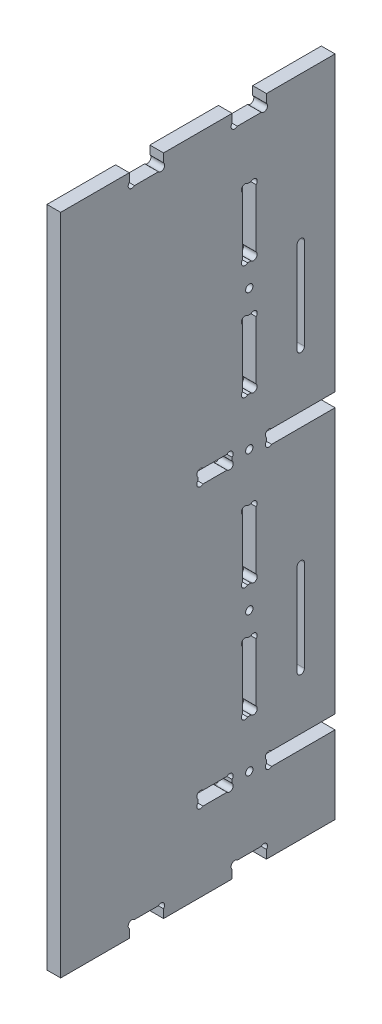
SolidWorks part; units mm, degrees
ref_plane "Plan de face" through (0, 0, 0) normal (0, 0, 1) x (1, 0, 0)
ref_plane "Plan de dessus" through (0, 0, 0) normal (0, 1, 0) x (1, 0, 0)
ref_plane "Plan de droite" through (0, 0, 0) normal (1, 0, 0) x (0, 0, -1)
sketch "Esquisse1" plane through (0, 0, 0) normal (1, 0, 0) x (0, 0, -1)
  line L0 (-10, 0) -> (130, 0) construction
  line L1 (0, -10) -> (0, 300) construction
  line L2 (120, -10) -> (120, 300) construction
  line L3 (130, 290) -> (-10, 290) construction
  line L4 (-20, 34) -> (140, 34) construction
  line L5 (-20, 40) -> (140, 40) construction
  line L6 (140, 156) -> (-20, 156) construction
  line L7 (-20, 162) -> (140, 162) construction
  line L8 (-10, 284) -> (130, 284) construction
  line L9 (130, 6) -> (-10, 6) construction
  line L10 (-20, 256) -> (140, 256) construction
  line L11 (60, 320.0265) -> (60, -23.3948) construction
  line L12 (-59.0456, 145) -> (66.7218, 145) construction
  line L13 (30, -9.1701) -> (30, 14.8573) construction
  line L14 (45, 11.6889) -> (45, -9.1701) construction
  line L15 (37.5, 2.4409) -> (37.5, -4.0751) construction
  line L16 (30, 6) -> (42.8913, -6.8913) construction
  line L17 (32.2627, 6) -> (42.7373, 6)
  line L18 (45, 3.7373) -> (45, 0)
  line L19 (30, 3.7373) -> (30, 0)
  line L20 (75, 3.7373) -> (75, 0)
  line L21 (87.7373, 6) -> (77.2627, 6)
  line L22 (90, 3.7373) -> (90, 0)
  line L23 (0, 0) -> (30, 0)
  line L24 (45, 0) -> (75, 0)
  line L25 (90, 0) -> (120, 0)
  line L26 (90, 290) -> (120, 290)
  line L27 (90, 286.2627) -> (90, 290)
  line L28 (87.7373, 284) -> (77.2627, 284)
  line L29 (75, 286.2627) -> (75, 290)
  line L30 (45, 290) -> (75, 290)
  line L31 (45, 286.2627) -> (45, 290)
  line L32 (32.2627, 284) -> (42.7373, 284)
  line L33 (30, 286.2627) -> (30, 290)
  line L34 (0, 290) -> (30, 290)
  line L35 (0, 290) -> (0, 0)
  line L36 (120, 0) -> (120, 34)
  line L37 (-20, 134) -> (66.7218, 134) construction
  line L38 (90, 310.1112) -> (90, -15.2075) construction
  line L39 (70.8381, 37) -> (93.292, 37) construction
  line L40 (79.681, 98) -> (87.7395, 98) construction
  line L41 (90, 34) -> (99.2543, 43.2543) construction
  line L42 (90, 37.7373) -> (90, 36.2627)
  line L43 (92.2627, 40) -> (120, 40)
  line L44 (92.2627, 34) -> (120, 34)
  line L45 (120, 40) -> (120, 156)
  line L46 (92.2627, 162) -> (120, 162)
  line L47 (92.2627, 156) -> (120, 156)
  line L48 (90, 158.2627) -> (90, 159.7373)
  line L49 (120, 162) -> (120, 290)
  line L50 (82.5, -10) -> (82.5, 300) construction
  line L51 (75, 43.6727) -> (75, 30.1815) construction
  line L52 (67.5, 38.4171) -> (67.5, 35.1314) construction
  line L53 (75, 37.7373) -> (75, 36.2627)
  line L54 (60, 37.7373) -> (60, 36.2627)
  line L55 (62.2627, 40) -> (72.7373, 40)
  line L56 (72.7373, 34) -> (62.2627, 34)
  line L57 (60, 158.2627) -> (60, 159.7373)
  line L58 (72.7373, 162) -> (62.2627, 162)
  line L59 (62.2627, 156) -> (72.7373, 156)
  line L60 (75, 158.2627) -> (75, 159.7373)
  line L61 (79.5, 164.7795) -> (79.5, 25.9693) construction
  line L62 (85.5, 164.7795) -> (85.5, 25.9693) construction
  line L63 (88.8686, 88) -> (51.1707, 88) construction
  line L64 (97.4677, 58) -> (51.1707, 58) construction
  line L65 (79.5, 88) -> (87.7395, 79.7605) construction
  line L66 (77.6869, 73) -> (86.5883, 73) construction
  line L67 (83.2373, 138) -> (81.7627, 138)
  line L68 (83.2373, 58) -> (81.7627, 58)
  line L69 (85.5, 60.2627) -> (85.5, 85.7373)
  line L70 (83.2373, 88) -> (81.7627, 88)
  line L71 (79.5, 60.2627) -> (79.5, 85.7373)
  line L72 (85.5, 135.7373) -> (85.5, 110.2627)
  line L73 (79.5, 135.7373) -> (79.5, 110.2627)
  line L74 (83.2373, 108) -> (81.7627, 108)
  line L75 (66.7218, 159) -> (108.1831, 159) construction
  line L76 (85.5, 257.7373) -> (85.5, 232.2627)
  line L77 (79.5, 257.7373) -> (79.5, 232.2627)
  line L78 (83.2373, 260) -> (81.7627, 260)
  line L79 (83.2373, 230) -> (81.7627, 230)
  line L80 (83.2373, 210) -> (81.7627, 210)
  line L81 (85.5, 182.2627) -> (85.5, 207.7373)
  line L82 (79.5, 182.2627) -> (79.5, 207.7373)
  line L83 (83.2373, 180) -> (81.7627, 180)
  line L84 (105, 325.8851) -> (105, -46.468) construction
  line L85 (170.2936, 84) -> (-38.142, 84) construction
  line L86 (170.2936, 206) -> (-16.5119, 206) construction
  line L87 (170.2936, 64) -> (94.9816, 64) construction
  line L88 (94.9816, 104) -> (170.2936, 104) construction
  line L89 (170.2936, 186) -> (94.9816, 186) construction
  line L90 (94.9816, 226) -> (170.2936, 226) construction
  line L91 (106.6, 104) -> (106.6, 64)
  line L92 (103.4, 64) -> (103.4, 104)
  line L93 (106.6, 226) -> (106.6, 186)
  line L94 (103.4, 186) -> (103.4, 226)
  line L98 (106.6, 234.8116) -> (106.6, 58) construction
  line L99 (103.4, 58) -> (103.4, 234.8116) construction
  arc A0 (32.2627, 6) -> (30, 3.7373) centre (31.1314, 4.8686) ccw
  arc A1 (42.7373, 6) -> (45, 3.7373) centre (43.8686, 4.8686) cw
  arc A2 (77.2627, 6) -> (75, 3.7373) centre (76.1314, 4.8686) ccw
  arc A3 (87.7373, 6) -> (90, 3.7373) centre (88.8686, 4.8686) cw
  arc A4 (87.7373, 284) -> (90, 286.2627) centre (88.8686, 285.1314) ccw
  arc A5 (77.2627, 284) -> (75, 286.2627) centre (76.1314, 285.1314) cw
  arc A6 (42.7373, 284) -> (45, 286.2627) centre (43.8686, 285.1314) ccw
  arc A7 (32.2627, 284) -> (30, 286.2627) centre (31.1314, 285.1314) cw
  arc A8 (90, 36.2627) -> (92.2627, 34) centre (91.1314, 35.1314) ccw
  arc A9 (90, 37.7373) -> (92.2627, 40) centre (91.1314, 38.8686) cw
  arc A10 (90, 158.2627) -> (92.2627, 156) centre (91.1314, 157.1314) ccw
  arc A11 (90, 159.7373) -> (92.2627, 162) centre (91.1314, 160.8686) cw
  circle A12 centre (82.5, 37) radius 1.6
  circle A13 centre (82.5, 159) radius 1.6
  arc A14 (75, 36.2627) -> (72.7373, 34) centre (73.8686, 35.1314) cw
  arc A15 (75, 37.7373) -> (72.7373, 40) centre (73.8686, 38.8686) ccw
  arc A16 (60, 36.2627) -> (62.2627, 34) centre (61.1314, 35.1314) ccw
  arc A17 (60, 37.7373) -> (62.2627, 40) centre (61.1314, 38.8686) cw
  arc A18 (60, 158.2627) -> (62.2627, 156) centre (61.1314, 157.1314) ccw
  arc A19 (60, 159.7373) -> (62.2627, 162) centre (61.1314, 160.8686) cw
  arc A20 (75, 158.2627) -> (72.7373, 156) centre (73.8686, 157.1314) cw
  arc A21 (75, 159.7373) -> (72.7373, 162) centre (73.8686, 160.8686) ccw
  arc A22 (81.7627, 88) -> (79.5, 85.7373) centre (80.6314, 86.8686) ccw
  arc A23 (83.2373, 88) -> (85.5, 85.7373) centre (84.3686, 86.8686) cw
  arc A24 (81.7627, 58) -> (79.5, 60.2627) centre (80.6314, 59.1314) cw
  arc A25 (83.2373, 58) -> (85.5, 60.2627) centre (84.3686, 59.1314) ccw
  arc A26 (81.7627, 138) -> (79.5, 135.7373) centre (80.6314, 136.8686) ccw
  arc A27 (83.2373, 138) -> (85.5, 135.7373) centre (84.3686, 136.8686) cw
  arc A28 (81.7627, 108) -> (79.5, 110.2627) centre (80.6314, 109.1314) cw
  arc A29 (83.2373, 108) -> (85.5, 110.2627) centre (84.3686, 109.1314) ccw
  circle A30 centre (82.5, 98) radius 1.6
  arc A31 (83.2373, 230) -> (85.5, 232.2627) centre (84.3686, 231.1314) ccw
  arc A32 (81.7627, 260) -> (79.5, 257.7373) centre (80.6314, 258.8686) ccw
  arc A33 (83.2373, 260) -> (85.5, 257.7373) centre (84.3686, 258.8686) cw
  arc A34 (81.7627, 230) -> (79.5, 232.2627) centre (80.6314, 231.1314) cw
  circle A35 centre (82.5, 220) radius 1.6
  arc A36 (81.7627, 210) -> (79.5, 207.7373) centre (80.6314, 208.8686) ccw
  arc A37 (83.2373, 210) -> (85.5, 207.7373) centre (84.3686, 208.8686) cw
  arc A38 (81.7627, 180) -> (79.5, 182.2627) centre (80.6314, 181.1314) cw
  arc A39 (83.2373, 180) -> (85.5, 182.2627) centre (84.3686, 181.1314) ccw
  arc A40 (103.4, 64) -> (106.6, 64) centre (105, 64) ccw
  arc A41 (106.6, 104) -> (103.4, 104) centre (105, 104) ccw
  arc A42 (103.4, 186) -> (106.6, 186) centre (105, 186) ccw
  arc A43 (106.6, 226) -> (103.4, 226) centre (105, 226) ccw
  dimension "D4" = 100
  dimension "D12" = 3
  dimension "D7" = 7.5
  dimension "D17" = 15
  dimension "D18" = 15
  dimension "D1" = 15
  dimension "D2" = 7.5
  dimension "D3" = 45
  dimension "D5" = 34
  dimension "D6" = 100
  dimension "D8" = 7.5
  dimension "D9" = 6
  dimension "D10" = 3
  dimension "D11" = 45
  dimension "D13" = 6
  dimension "D14" = 10
  dimension "D15" = 30
  dimension "D16" = 45
  dimension "D19" = 50
  dimension "D20" = 50
  dimension "D21" = 20
  dimension "D22" = 20
  dimension "D23" = 20
  dimension "D24" = 20
  dimension "D32" = 1.6
  dimension "D33" = 3.2
extrude "Extrusion1" add sketch "Esquisse1" along normal blind 6
sketch "Esquisse2" plane through (0, 0, 0) normal (-1, 0, 0) x (0, 0, 1)
  line L0 (-116, 41.88) -> (-116, 169.3736) construction
  line L1 (-105, 142.8726) -> (-105, 52.1455) construction
  line L2 (-117.55, 276.9953) -> (-117.55, 41.88) construction
  line L3 (-114.45, 276.9953) -> (-114.45, 41.88) construction
  line L4 (-138.8552, 84) -> (-63.7346, 84) construction
  line L5 (-117.55, 123) -> (-117.55, 45)
  line L6 (-138.8552, 108) -> (-110.4584, 108) construction
  line L7 (-114.45, 45) -> (-114.45, 123)
  line L8 (-138.8552, 60) -> (-110.4584, 60) construction
  line L9 (-120, 40) -> (-120, 156) construction
  line L10 (-56.165, 159) -> (-29.1969, 159) construction
  line L11 (-95.55, 45) -> (-95.55, 123)
  line L12 (-92.45, 123) -> (-92.45, 45)
  line L13 (47.9717, 34) -> (-172.0336, 34) construction
  line L14 (-169.0565, 134) -> (47.9717, 134) construction
  line L15 (47.9717, 156) -> (-169.0565, 156) construction
  line L16 (-63.7346, 206) -> (-138.8552, 206) construction
  line L18 (-129.6973, 167) -> (-100.1112, 167) construction
  line L19 (-117.55, 245) -> (-117.55, 167)
  line L20 (-114.45, 167) -> (-114.45, 245)
  line L21 (-125.7229, 45) -> (-89.9825, 45) construction
  line L22 (-95.55, 167) -> (-95.55, 245)
  line L23 (-92.45, 245) -> (-92.45, 167)
  arc A0 (-117.55, 123) -> (-114.45, 123) centre (-116, 123) cw
  arc A1 (-117.55, 45) -> (-114.45, 45) centre (-116, 45) ccw
  arc A2 (-92.45, 45) -> (-95.55, 45) centre (-94, 45) cw
  arc A3 (-92.45, 123) -> (-95.55, 123) centre (-94, 123) ccw
  arc A4 (-117.55, 167) -> (-114.45, 167) centre (-116, 167) ccw
  arc A5 (-117.55, 245) -> (-114.45, 245) centre (-116, 245) cw
  arc A6 (-92.45, 167) -> (-95.55, 167) centre (-94, 167) cw
  arc A7 (-92.45, 245) -> (-95.55, 245) centre (-94, 245) ccw
  dimension "D1" = 15
  dimension "D2" = 11
  dimension "D3" = 24
  dimension "D4" = 24
  dimension "D5" = 15
  dimension "D6" = 39
  dimension "D7" = 1.55
  dimension "D8" = 3.1
extrude "Enlèv. mat.-Extru.1" cut sketch "Esquisse2" against normal blind 2.2
